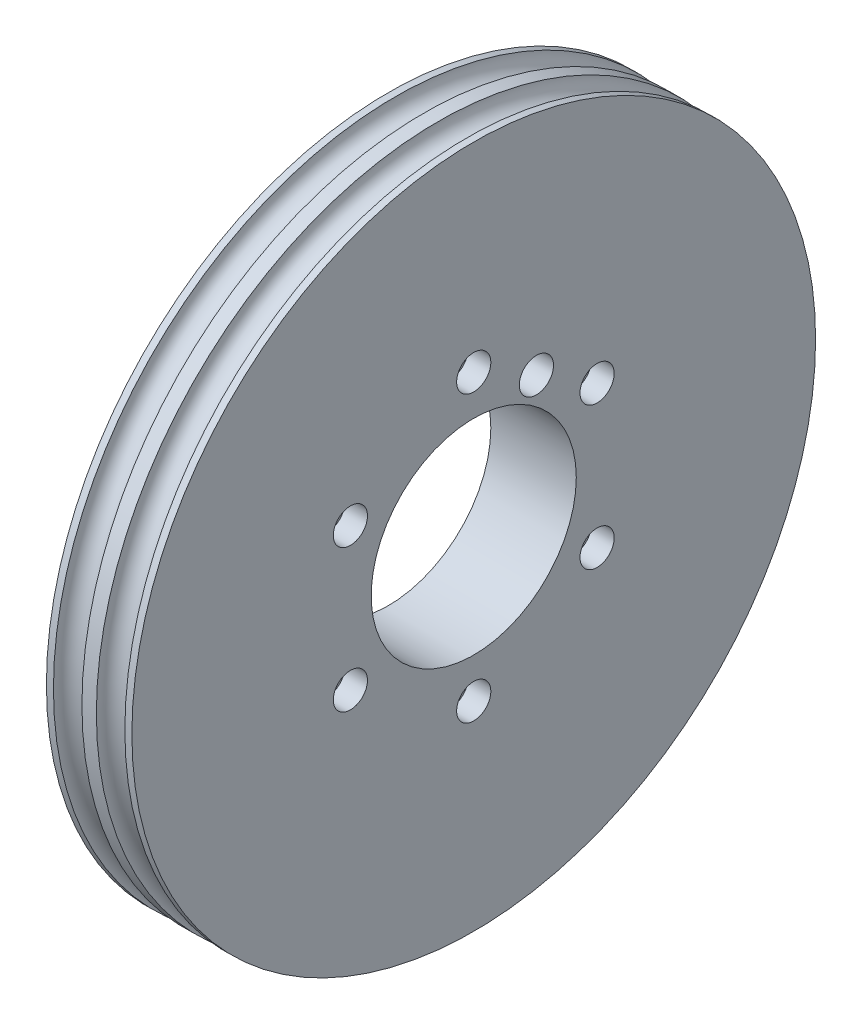
SolidWorks part; units mm, degrees
ref_plane "Front Plane" through (0, 0, 0) normal (0, 0, 1) x (1, 0, 0)
ref_plane "Top Plane" through (0, 0, 0) normal (0, 1, 0) x (1, 0, 0)
ref_plane "Right Plane" through (0, 0, 0) normal (1, 0, 0) x (0, 0, -1)
sketch "Sketch1" plane through (0, 0, 0) normal (1, 0, 0) x (0, 0, -1)
  circle A0 centre (0, 0) radius 18
  circle A1 centre (0, 0) radius 60
  dimension "D1" = 36
  dimension "D2" = 120
extrude "Boss-Extrude1" add sketch "Sketch1" along normal mid plane 15
sketch "Sketch3" plane through (7.5, 0, 0) normal (1, 0, 0) x (0, 0, -1)
  line L0 (0, 0) -> (0, 25) construction
  circle A0 centre (0, 25) radius 2
  circle A1 centre (21.6506, 12.5) radius 2
  circle A2 centre (21.6506, -12.5) radius 2
  circle A3 centre (0, -25) radius 2
  circle A4 centre (-21.6506, -12.5) radius 2
  circle A5 centre (-21.6506, 12.5) radius 2
  point P20 (0, 0)
  dimension "D1" = 25
  dimension "D2" = 6
extrude "Cut-Extrude2" cut sketch "Sketch3" against normal up to next
sketch "Sketch4" plane through (-7.5, 0, 0) normal (-1, 0, 0) x (0, 0, 1)
  circle A0 centre (0, 0) radius 31.5
  circle A1 centre (0, 0) radius 33
  circle A2 centre (0, 0) radius 30
  dimension "D1" = 1.5
  dimension "D2" = 1.5
extrude "Cut-Extrude3" cut sketch "Sketch4" against normal blind 3 contours A1 A0 | A0 A2
sketch "Sketch5" plane through (0, 0, 0) normal (0, 0, 1) x (1, 0, 0)
  line L0 (0, 58.4096) -> (0, 61.7624) construction
  line L1 (0, -60) -> (0, 60) construction
  line L7 (7.5338, 60.0138) -> (0, 60.0138) construction
  circle A0 centre (3.7669, 60.0138) radius 2.5
  circle A1 centre (-3.7669, 60.0138) radius 2.5
  point P9 (3.7669, 60.0138)
  dimension "D1" = 5
ref_axis "Axis1" through (7.5, 0, 0) along (-1, 0, 0)
revolve "Cut-Revolve2" cut sketch "Sketch5" angle 360 about axis through (7.5, 0, 0) along (-1, 0, 0)
sketch "Sketch6" plane through (7.5, 0, 0) normal (1, 0, 0) x (0, 0, -1)
  circle A8 centre (0, 25) radius 3
  circle A9 centre (21.6506, 12.5) radius 3
  circle A10 centre (21.6506, -12.5) radius 3
  circle A11 centre (0, -25) radius 3
  circle A12 centre (-21.6506, -12.5) radius 3
  circle A13 centre (-21.6506, 12.5) radius 3
  point P16 (0, 0)
extrude "Cut-Extrude4" cut sketch "Sketch6" against normal blind 4
sketch "Sketch7" plane through (-7.5, 0, 0) normal (-1, 0, 0) x (0, 0, 1)
  line L0 (0, 0) -> (-11, 19.0526) construction
  line L1 (0, 0) -> (0, 2.9604) construction
  circle A1 centre (-11, 19.0526) radius 3
  point P11 (0, 0)
  dimension "D1" = 30
  dimension "D3" = 22
extrude "Cut-Extrude5" cut sketch "Sketch7" against normal up to next
